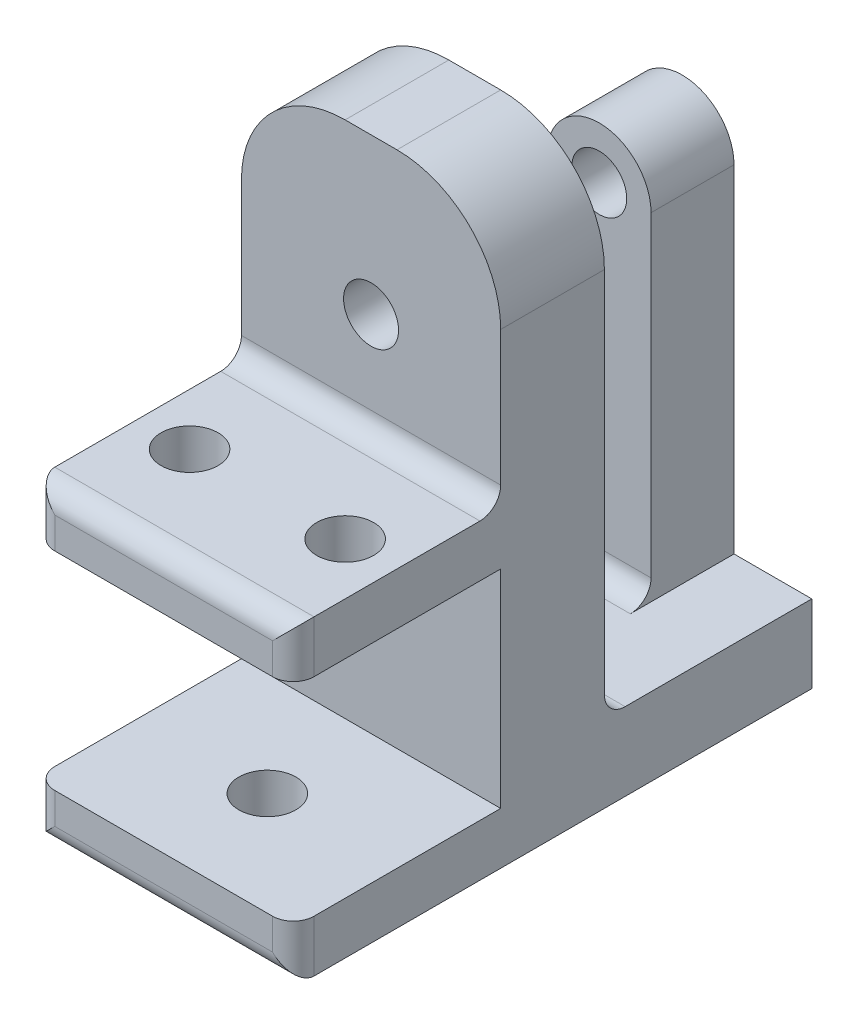
SolidWorks part; units mm, degrees
ref_plane "Front Plane" through (0, 0, 0) normal (0, 0, 1) x (1, 0, 0)
ref_plane "Top Plane" through (0, 0, 0) normal (0, 1, 0) x (1, 0, 0)
ref_plane "Right Plane" through (0, 0, 0) normal (1, 0, 0) x (0, 0, -1)
sketch "Sketch1" plane through (0, 0, 0) normal (0, 0, 1) x (1, 0, 0)
  line L0 (0, 20) -> (25, 20) construction
  line L1 (0, 0) -> (25, 0)
  line L2 (0, 0) -> (0, 40)
  line L3 (10, 50) -> (15, 50)
  line L4 (25, 0) -> (25, 40)
  line L5 (0, 20) -> (25, 50) construction
  line L6 (25, 20) -> (0, 50) construction
  circle A0 centre (12.5, 35) radius 2.65
  arc A1 (15, 50) -> (25, 40) centre (15, 40) cw
  arc A2 (0, 40) -> (10, 50) centre (10, 40) cw
  dimension "D2" = 5.3
  dimension "D5" = 10
  dimension "D1" = 20
  dimension "D3" = 50
  dimension "D4" = 25
extrude "Boss-Extrude1" add sketch "Sketch1" along normal blind 10
sketch "Sketch2" plane through (0, 0, 0) normal (0, -1, 0) x (1, 0, 0)
  line L0 (0, 10) -> (25, 10) construction
  line L1 (0, 10) -> (25, 10)
  line L2 (0, 10) -> (0, 30)
  line L3 (0, 30) -> (25, 30)
  line L4 (25, 10) -> (25, 30)
  line L5 (0, 10) -> (0, 0) construction
  dimension "D1" = 20
extrude "Boss-Extrude2" add sketch "Sketch2" against normal blind 5 from offset 20 offset against normal yes
sketch "Sketch3" plane through (0, 0, 0) normal (0, -1, 0) x (1, 0, 0)
  line L0 (0, 0) -> (25, 0) construction
  line L1 (25, 0) -> (25, 10) construction
  line L3 (0, 10) -> (0, 0) construction
  line L4 (0, 30) -> (0, 10) construction
  line L6 (25, 10) -> (25, 30) construction
  line L7 (25, 30) -> (0, 30) construction
  line L8 (0, 0) -> (25, 0)
  line L9 (25, 0) -> (25, 10)
  line L11 (0, 10) -> (0, 0)
  line L12 (0, 30) -> (0, 10)
  line L14 (25, 10) -> (25, 30)
  line L15 (25, 30) -> (0, 30)
extrude "Boss-Extrude3" add sketch "Sketch3" along normal blind 5
sketch "Sketch4" plane through (0, 0, 0) normal (0, 0, -1) x (-1, 0, 0)
  line L0 (0, 40) -> (0, -5) construction
  line L1 (-25, -5) -> (0, -5)
  line L2 (-25, -5) -> (-25, 2.5)
  line L3 (-25, 2.5) -> (0, 2.5)
  line L4 (0, -5) -> (0, 2.5)
  dimension "D1" = 7.5
extrude "Boss-Extrude4" add sketch "Sketch4" along normal blind 20
sketch "Sketch5" plane through (0, 0, -20) normal (0, 0, -1) x (-1, 0, 0)
  line L0 (-17.5, 2.5) -> (-17.5, 22.5)
  line L1 (-17.5, 2.5) -> (-7.5, 2.5)
  line L2 (-17.5, 22.5) -> (-7.5, 22.5)
  line L3 (-7.5, 2.5) -> (-7.5, 22.5)
  line L5 (0, 2.5) -> (-25, 2.5) construction
  line L6 (-12.5, 35) -> (-12.5, 2.5) construction
  line L7 (0, 2.5) -> (-25, 2.5) construction
  point P9 (-4.0336, 2.5)
  dimension "D1" = 10
  dimension "D2" = 20
extrude "Boss-Extrude5" add sketch "Sketch5" against normal blind 8
fillet "Fillet2" radius 2 2 edges at (12.5, 2.5, 0) (12.5, 2.5, -12)
sketch "Sketch6" plane through (0, 25, 0) normal (0, 1, 0) x (1, 0, 0)
  line L0 (0, -20) -> (25, -20) construction
  line L1 (0, -30) -> (0, -10) construction
  line L2 (25, -10) -> (25, -30) construction
  line L3 (12.5, -10) -> (12.5, -20) construction
  line L4 (15, -10) -> (10, -10) construction
  circle A0 centre (5, -20) radius 2.75
  circle A1 centre (20, -20) radius 2.75
  dimension "D1" = 5.5
  dimension "D2" = 15
extrude "Cut-Extrude1" cut sketch "Sketch6" against normal blind 6
sketch "Sketch7" plane through (0, -5, 0) normal (0, -1, 0) x (1, 0, 0)
  line L0 (0, 20) -> (25, 20) construction
  line L1 (0, 30) -> (0, -20) construction
  line L2 (25, -20) -> (25, 30) construction
  line L3 (0, 30) -> (0, 10) construction
  circle A0 centre (12.5, 20) radius 2.75
  circle A1 centre (5, 20) radius 2.75 construction
  point P8 (0, 20)
extrude "Cut-Extrude2" cut sketch "Sketch7" against normal blind 6
sketch "Sketch8" plane through (0, 0, -20) normal (0, 0, -1) x (-1, 0, 0)
  line L0 (-17.5, 22.5) -> (-17.5, 35)
  line L2 (-7.5, 22.5) -> (-17.5, 22.5) construction
  line L3 (-7.5, 35) -> (-7.5, 22.5)
  line L4 (-7.5, 22.5) -> (-17.5, 22.5)
  arc A0 (-17.5, 35) -> (-7.5, 35) centre (-12.5, 35) cw
extrude "Boss-Extrude6" add sketch "Sketch8" against normal up to vertex
sketch "Sketch9" plane through (0, 0, -20) normal (0, 0, -1) x (-1, 0, 0)
  circle A0 centre (-12.5, 35) radius 2.65 construction
  circle A1 centre (-12.5, 35) radius 2.65
extrude "Cut-Extrude3" cut sketch "Sketch9" against normal blind 50
fillet "Fillet4" radius 2 1 edges at (12.5, 25, 10)
fillet "Fillet6" radius 2 6 edges at (0, 22.5, 30) (25, 22.5, 30) (0, -2.5, 30) (25, -2.5, 30) (12.5, -5, 30) (12.5, 25, 30)
